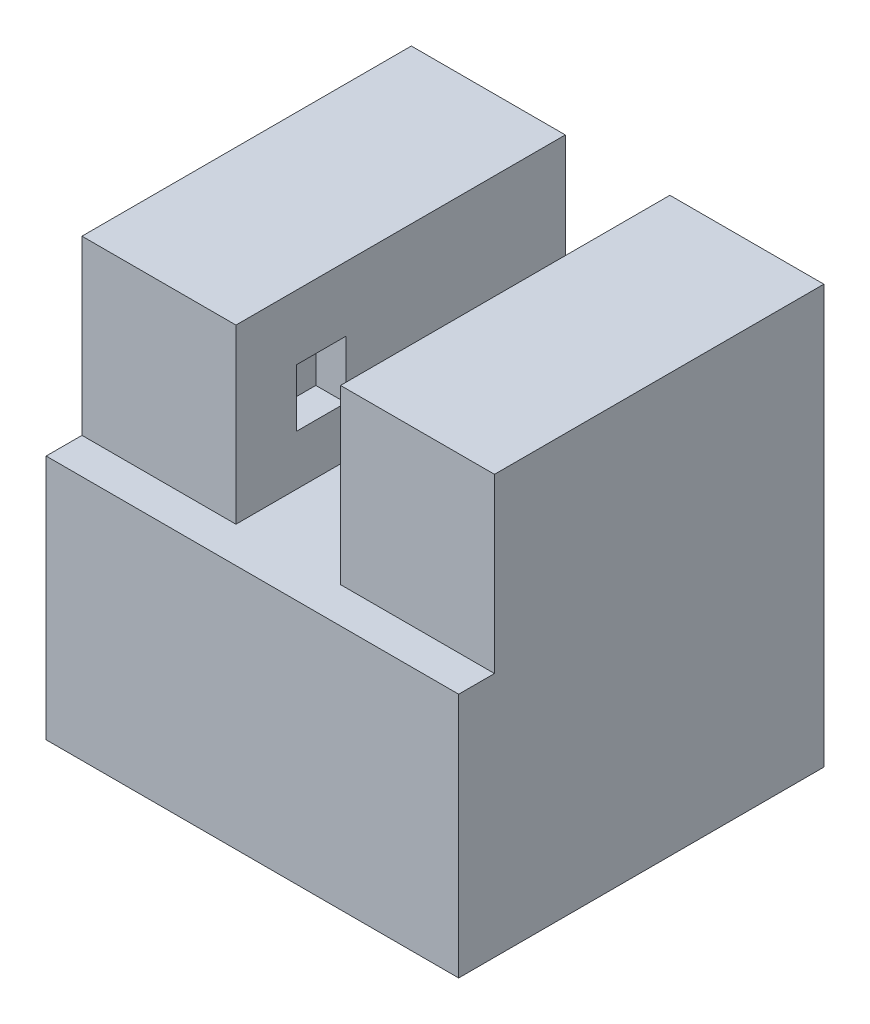
SolidWorks part; units mm, degrees
ref_plane "Front Plane" through (0, 0, 0) normal (0, 0, 1) x (1, 0, 0)
ref_plane "Top Plane" through (0, 0, 0) normal (0, 1, 0) x (1, 0, 0)
ref_plane "Right Plane" through (0, 0, 0) normal (1, 0, 0) x (0, 0, -1)
sketch "Sketch2" plane through (0, 0, 0) normal (0, 1, 0) x (1, 0, 0)
  line L1 (-9.35, 10) -> (9.35, 10)
  line L2 (-9.35, 10) -> (-9.35, -10)
  line L3 (-9.35, -10) -> (9.35, -10)
  line L4 (9.35, 10) -> (9.35, -10)
  point P4 (0, 10)
  point P6 (-9.35, 0)
  dimension "D1" = 18.7
  dimension "D2" = 20
extrude "Boss-Extrude1" add sketch "Sketch2" along normal blind 25.4
sketch "Sketch3" plane through (0, 0, -10) normal (0, 0, -1) x (-1, 0, 0)
  line L0 (-9.35, 25.4) -> (9.35, 25.4) construction
  line L1 (-3.175, 25.4) -> (3.175, 25.4)
  line L2 (-3.175, 25.4) -> (-3.175, 18.1)
  line L3 (-3.175, 18.1) -> (3.175, 18.1)
  line L4 (3.175, 25.4) -> (3.175, 18.1)
  line L5 (-9.35, 22.225) -> (9.35, 22.225) construction
  line L6 (-9.35, 25.4) -> (-9.35, 0) construction
  line L7 (9.35, 25.4) -> (9.35, 0) construction
  line L9 (-3.175, 18.1) -> (3.175, 18.1)
  line L10 (-3.175, 18.1) -> (-3.175, 14.925)
  line L11 (-3.175, 14.925) -> (3.175, 14.925)
  line L12 (3.175, 18.1) -> (3.175, 14.925)
  point P6 (0, 18.1)
  point P9 (6.0716, 19.725)
  line M12 (9.35, 25.4) -> (-9.35, 25.4)
  dimension "D1" = 6.35
  dimension "D2" = 3.175
  dimension "D3" = 2.5
  dimension "D4" = 1.625
  dimension "D5" = 3.175
extrude "Cut-Extrude1" cut sketch "Sketch3" against normal through all contours L12 L3 L10 L11 | L5 L2 L3 L4 | L2 L5 L4 M12
sketch "Sketch5" plane through (0, 0, -10) normal (0, 0, -1) x (-1, 0, 0)
  line L0 (9.35, 25.4) -> (9.35, 0) construction
  line L1 (-9.35, 25.4) -> (-12.525, 25.4)
  line L2 (-9.35, 25.4) -> (-9.35, 0)
  line L3 (-9.35, 0) -> (-12.525, 0)
  line L4 (-12.525, 25.4) -> (-12.525, 0)
  line L5 (9.35, 25.4) -> (12.525, 25.4)
  line L6 (9.35, 25.4) -> (9.35, 0)
  line L7 (9.35, 0) -> (12.525, 0)
  line L8 (12.525, 25.4) -> (12.525, 0)
  line L9 (-9.35, 0) -> (9.35, 0) construction
  dimension "D1" = 3.175
extrude "Boss-Extrude2" add sketch "Sketch5" against normal up to surface (20 mm away) up to face at (0, 16.4312, 10)
sketch "Sketch6" plane through (0, 0, -10) normal (0, 0, -1) x (-1, 0, 0)
  line L0 (-12.525, 0) -> (12.525, 0) construction
  line L1 (-9.35, 22.225) -> (-5, 22.225)
  line L2 (-9.35, 22.225) -> (-9.35, 0)
  line L3 (-9.35, 0) -> (-5, 0)
  line L4 (-5, 22.225) -> (-5, 0)
  line L5 (-3.175, 14.925) -> (3.175, 14.925) construction
  line L6 (-5, 10.125) -> (5, 10.125)
  line L7 (-5, 10.125) -> (-5, 0)
  line L8 (-5, 0) -> (5, 0)
  line L9 (5, 10.125) -> (5, 0)
  line L10 (9.35, 0) -> (5, 0)
  line L11 (9.35, 0) -> (9.35, 22.225)
  line L12 (9.35, 22.225) -> (5, 22.225)
  line L13 (5, 0) -> (5, 22.225)
  line L14 (-12.525, 25.4) -> (-3.175, 25.4) construction
  point P12 (0, 10.125)
  point P15 (0, 14.925)
  line M18 (-12.525, 0) -> (12.525, 0)
  dimension "D1" = 10
  dimension "D2" = 18.7
  dimension "D3" = 3.175
  dimension "D4" = 12.1
extrude "Cut-Extrude2" cut sketch "Sketch6" against normal blind 16.825 contours L13 L9 L11 L12 M18 | L9 L6 L4 M18 | L4 L1 L2 M18
sketch "Sketch7" plane through (5, 0, 0) normal (1, 0, 0) x (0, 0, -1)
  line L0 (-6.825, 22.225) -> (-6.825, 10.125) construction
  line L1 (-6.325, 21.475) -> (-3.325, 21.475)
  line L2 (-6.325, 21.475) -> (-6.325, 17.975)
  line L3 (-6.325, 17.975) -> (-3.325, 17.975)
  line L4 (-3.325, 21.475) -> (-3.325, 17.975)
  line L5 (-6.825, 22.225) -> (10, 22.225) construction
  point P6 (-4.825, 17.975)
  point P7 (-6.325, 19.725)
  dimension "D1" = 3
  dimension "D2" = 2
  dimension "D3" = 2.5
  dimension "D4" = 3.5
extrude "Cut-Extrude3" cut sketch "Sketch7" against normal up to surface (10 mm away) up to face at (-5, 16.175, -1.5875)
sketch "Sketch8" plane through (0, 0, -10) normal (0, 0, -1) x (-1, 0, 0)
  line L0 (9.35, 0) -> (12.525, 0) construction
  line L1 (-11, 10.125) -> (11, 10.125)
  line L2 (-11, 10.125) -> (-11, 0)
  line L3 (-11, 0) -> (11, 0)
  line L4 (11, 10.125) -> (11, 0)
  line L5 (-5, 10.125) -> (5, 10.125) construction
  point P9 (0, 10.125)
  dimension "D1" = 22
extrude "Cut-Extrude4" cut sketch "Sketch8" against normal blind 19
sketch "Sketch9" plane through (12.525, 0, 0) normal (1, 0, 0) x (0, 0, -1)
  line L0 (-10, 0) -> (-10, 25.4) construction
  line L1 (-10, 14.925) -> (-12.175, 14.925)
  line L2 (-10, 14.925) -> (-10, 0)
  line L3 (-10, 0) -> (-12.175, 0)
  line L4 (-12.175, 14.925) -> (-12.175, 0)
  line L5 (-10, 0) -> (10, 0) construction
  point P8 (0, 0)
  point P9 (0, 0)
  dimension "D1" = 3.175
extrude "Boss-Extrude3" add sketch "Sketch9" against normal up to surface (25.05 mm away) up to face at (-12.525, 12.7, 0)
